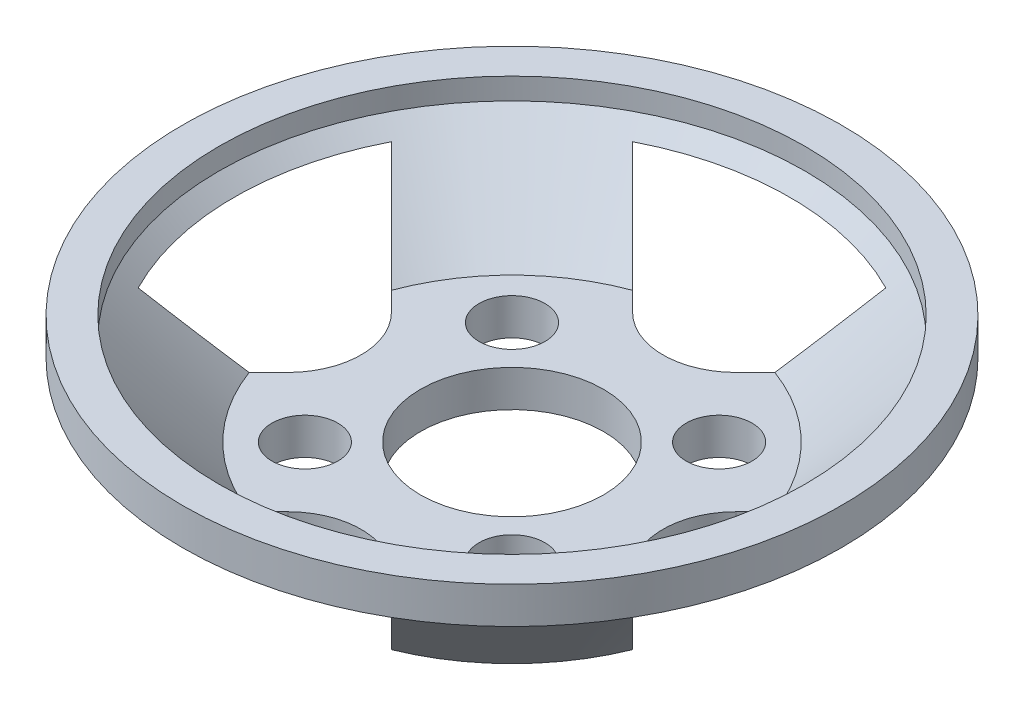
SolidWorks part; units mm, degrees
ref_plane "Ön Düzlem" through (0, 0, 0) normal (0, 0, 1) x (1, 0, 0)
ref_plane "Üst Düzlem" through (0, 0, 0) normal (0, 1, 0) x (1, 0, 0)
ref_plane "Sağ Düzlem" through (0, 0, 0) normal (1, 0, 0) x (0, 0, -1)
sketch "Çizim1" plane through (0, 0, 0) normal (0, 1, 0) x (1, 0, 0)
  circle A0 centre (0, 0) radius 9
  dimension "D1" = 18
extrude "Yükseklik-Ekstrüzyon1" add sketch "Çizim1" along normal blind 4
chamfer "Pah1" distance 3 angle 45 1 edges at (0, 0, 9)
shell "İç Boşaltma1" thickness 1
sketch "Çizim2" plane through (0, 0, 0) normal (0, -1, 0) x (1, 0, 0)
  line L0 (-4.5, 7.7942) -> (-1.4142, 4.7084)
  line L1 (1.4142, 4.7084) -> (4.5, 7.7942)
  line L2 (0, 0) -> (0, 9) construction
  line L3 (7.7942, 4.5) -> (4.7084, 1.4142)
  line L4 (4.7084, -1.4142) -> (7.7942, -4.5)
  line L5 (4.5, -7.7942) -> (1.4142, -4.7084)
  line L6 (-1.4142, -4.7084) -> (-4.5, -7.7942)
  line L7 (-7.7942, -4.5) -> (-4.7084, -1.4142)
  line L8 (-4.7084, 1.4142) -> (-7.7942, 4.5)
  circle A0 centre (0, 0) radius 2.5
  circle A1 centre (0, 0) radius 9 construction
  arc A2 (4.5, 7.7942) -> (-4.5, 7.7942) centre (0, 0) ccw
  arc A3 (-1.4142, 4.7084) -> (1.4142, 4.7084) centre (0, 6.1227) ccw
  arc A4 (7.7942, -4.5) -> (7.7942, 4.5) centre (0, 0) ccw
  arc A5 (4.7084, 1.4142) -> (4.7084, -1.4142) centre (6.1227, 0) ccw
  arc A6 (-4.5, -7.7942) -> (4.5, -7.7942) centre (0, 0) ccw
  arc A7 (1.4142, -4.7084) -> (-1.4142, -4.7084) centre (0, -6.1227) ccw
  arc A8 (-7.7942, 4.5) -> (-7.7942, -4.5) centre (0, 0) ccw
  arc A9 (-4.7084, -1.4142) -> (-4.7084, 1.4142) centre (-6.1227, 0) ccw
  point P12 (0, 3.2942)
  point P30 (0, 0)
  dimension "D1" = 5
  dimension "D6" = 2
  dimension "D2" = 45
  dimension "D3" = 45
  dimension "D4" = 4.5
  dimension "D5" = 4.5
  dimension "D7" = 4
extrude "Kes-Ekstrüzyon1" cut sketch "Çizim2" against normal blind 3
sketch "Çizim3" plane through (0, 0, 0) normal (0, -1, 0) x (1, 0, 0)
  line L0 (0, 0) -> (-4.2426, 4.2426) construction
  circle A0 centre (-2.8284, 2.8284) radius 0.9
  arc A1 (-2.2627, 5.557) -> (-5.557, 2.2627) centre (0, 0) ccw construction
  circle A2 centre (2.8284, 2.8284) radius 0.9
  circle A3 centre (2.8284, -2.8284) radius 0.9
  circle A4 centre (-2.8284, -2.8284) radius 0.9
  point P17 (0, 0)
  dimension "D2" = 1.8
  dimension "D1" = 4
  dimension "D3" = 4
extrude "Kes-Ekstrüzyon2" cut sketch "Çizim3" against normal blind 1
